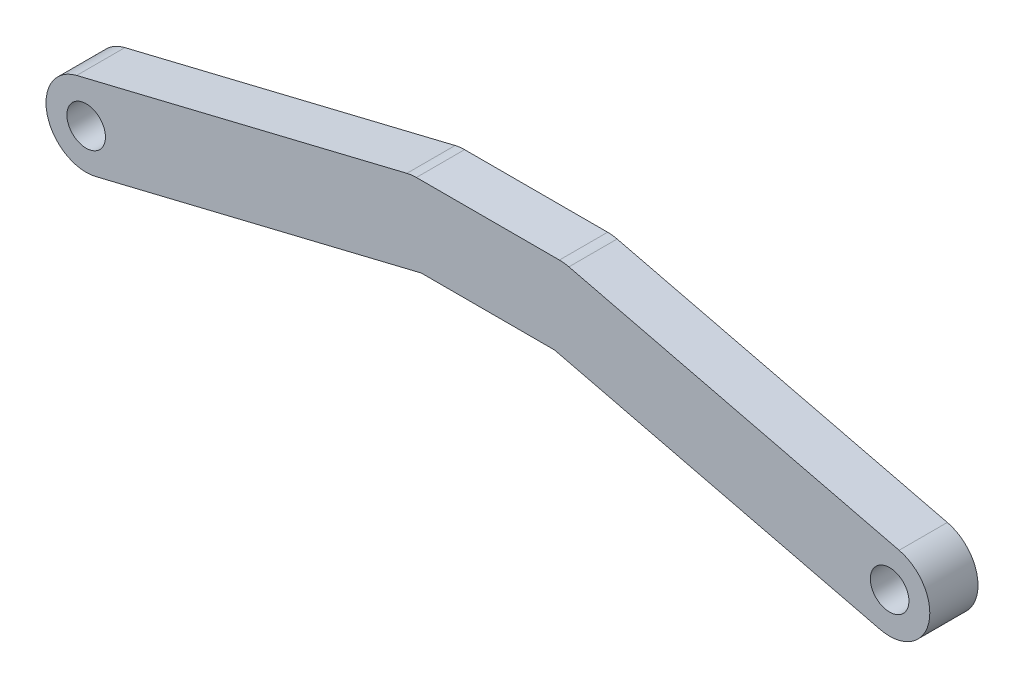
SolidWorks part; units mm, degrees
ref_plane "Front Plane" through (0, 0, 0) normal (0, 0, 1) x (1, 0, 0)
ref_plane "Top Plane" through (0, 0, 0) normal (0, 1, 0) x (1, 0, 0)
ref_plane "Right Plane" through (0, 0, 0) normal (1, 0, 0) x (0, 0, -1)
sketch "Sketch1" plane through (0, 0, 0) normal (0, 0, 1) x (1, 0, 0)
  line L0 (-25, 2.5) -> (25, 2.5)
  line L1 (-25, -2.5) -> (25, -2.5)
  line L2 (-25, 0) -> (25, 0) construction
  line L3 (-25, 0) -> (-4.4501, 5) construction
  line L4 (-4.4501, 5) -> (4.4501, 5) construction
  line L5 (4.4501, 5) -> (25, 0) construction
  line L6 (-25, 0) -> (-4.4501, 5) construction
  line L7 (-25.591, 2.4291) -> (-5.0412, 7.4291)
  line L8 (-24.409, -2.4291) -> (-3.8591, 2.5709)
  line L9 (25, 0) -> (4.4501, 5) construction
  line L10 (24.409, -2.4291) -> (3.8591, 2.5709)
  line L11 (25.591, 2.4291) -> (5.0412, 7.4291)
  line L12 (4.4501, 5) -> (-4.4501, 5) construction
  line L13 (4.4501, 2.5) -> (-4.4501, 2.5)
  line L14 (4.4501, 7.5) -> (-4.4501, 7.5)
  circle A0 centre (-25, 0) radius 1.2
  circle A1 centre (-25, 0) radius 2.5
  circle A2 centre (25, 0) radius 1.2
  circle A3 centre (25, 0) radius 2.5
  arc A4 (-25.591, 2.4291) -> (-24.409, -2.4291) centre (-25, 0) ccw
  arc A5 (-3.8591, 2.5709) -> (-5.0412, 7.4291) centre (-4.4501, 5) ccw
  arc A6 (24.409, -2.4291) -> (25.591, 2.4291) centre (25, 0) ccw
  arc A7 (5.0412, 7.4291) -> (3.8591, 2.5709) centre (4.4501, 5) ccw
  arc A8 (4.4501, 2.5) -> (4.4501, 7.5) centre (4.4501, 5) ccw
  arc A9 (-4.4501, 7.5) -> (-4.4501, 2.5) centre (-4.4501, 5) ccw
  point P10 (0, 0)
  point P11 (-14.7251, 2.5)
  point P19 (14.7251, 2.5)
  point P24 (0, 5)
  dimension "D1" = 2.4
  dimension "D2" = 5
  dimension "D3" = 5
  dimension "D5" = 2.4
  dimension "D4" = 50
  dimension "D6" = 5
extrude "Boss-Extrude1" add sketch "Sketch1" along normal mid plane 3 contours A7 L14 A5 L8 L0 L10 | A5 A9 L0 L8 | L0 A8 A7 L10 | A8 L0 A3 L11 | A3 L0 L10 | A3 A2 | A9 L7 A1 L0 | A1 L8 L0 | A1 A0
